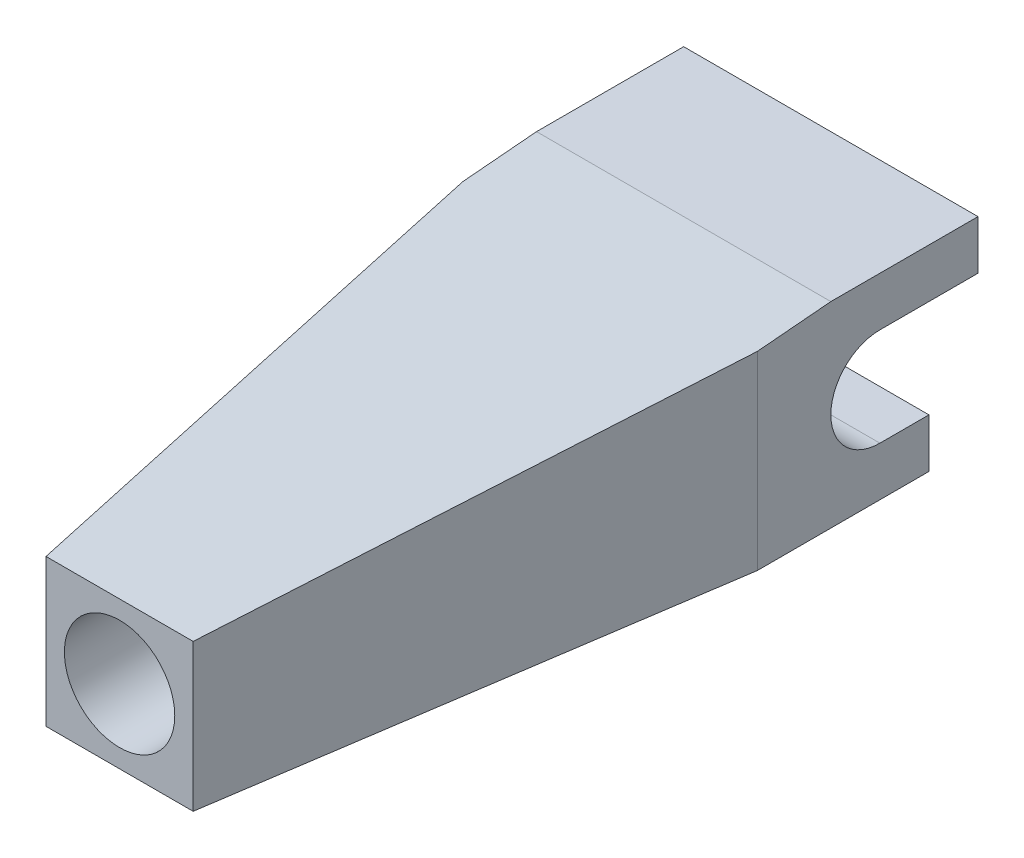
SolidWorks part; units mm, degrees
ref_plane "Спереди" through (0, 0, 0) normal (0, 0, 1) x (1, 0, 0)
ref_plane "Сверху" through (0, 0, 0) normal (0, 1, 0) x (1, 0, 0)
ref_plane "Справа" through (0, 0, 0) normal (1, 0, 0) x (0, 0, -1)
sketch "Эскиз1" plane through (0, 0, 0) normal (1, 0, 0) x (0, 0, -1)
  line L0 (0, 0) -> (25, 0) construction
  line L1 (0, 2) -> (0, -4)
  line L2 (0, 2) -> (23, 4)
  line L3 (23, 4) -> (29, 4)
  line L4 (29, 4) -> (29, 2)
  line L5 (25, 2) -> (29, 2)
  line L6 (25, -2) -> (27, -2)
  line L7 (27, -2) -> (27, -4)
  line L8 (27, -4) -> (0, -4)
  arc A0 (25, 2) -> (25, -2) centre (25, 0) ccw
  point P6 (29, 3)
  dimension "D1" = 4
  dimension "D2" = 2
  dimension "D3" = 2
  dimension "D4" = 2
  dimension "D5" = 2
  dimension "D6" = 2
  dimension "D7" = 6
  dimension "D8" = 23
  dimension "D9" = 6
extrude "Бобышка-Вытянуть1" add sketch "Эскиз1" along normal blind 12
sketch "Эскиз2" plane through (0, 4, 0) normal (0, 1, 0) x (1, 0, 0)
  line L0 (0, 0) -> (0, 20)
  line L1 (0, 23) -> (0, 0) construction
  line L2 (0, 20) -> (3, 0)
  line L3 (12, 0) -> (0, 0) construction
  line L4 (3, 0) -> (0, 0)
  line L5 (12, 20) -> (9, 0)
  line L6 (12, 23) -> (12, 0) construction
  line L7 (9, 0) -> (12, 0)
  line L8 (12, 0) -> (12, 20)
  dimension "D1" = 20
  dimension "D2" = 3
extrude "Вырез-Вытянуть1" cut sketch "Эскиз2" against normal through all
sketch "Эскиз3" plane through (0, 0, 0) normal (0, 0, 1) x (1, 0, 0)
  line L0 (3, -1) -> (9, -1) construction
  line L1 (3, -4) -> (3, 2) construction
  line L2 (9, -4) -> (9, 2) construction
  circle A0 centre (6, -1) radius 2.25
  dimension "D1" = 4.5
extrude "Вырез-Вытянуть2" cut sketch "Эскиз3" against normal blind 20
